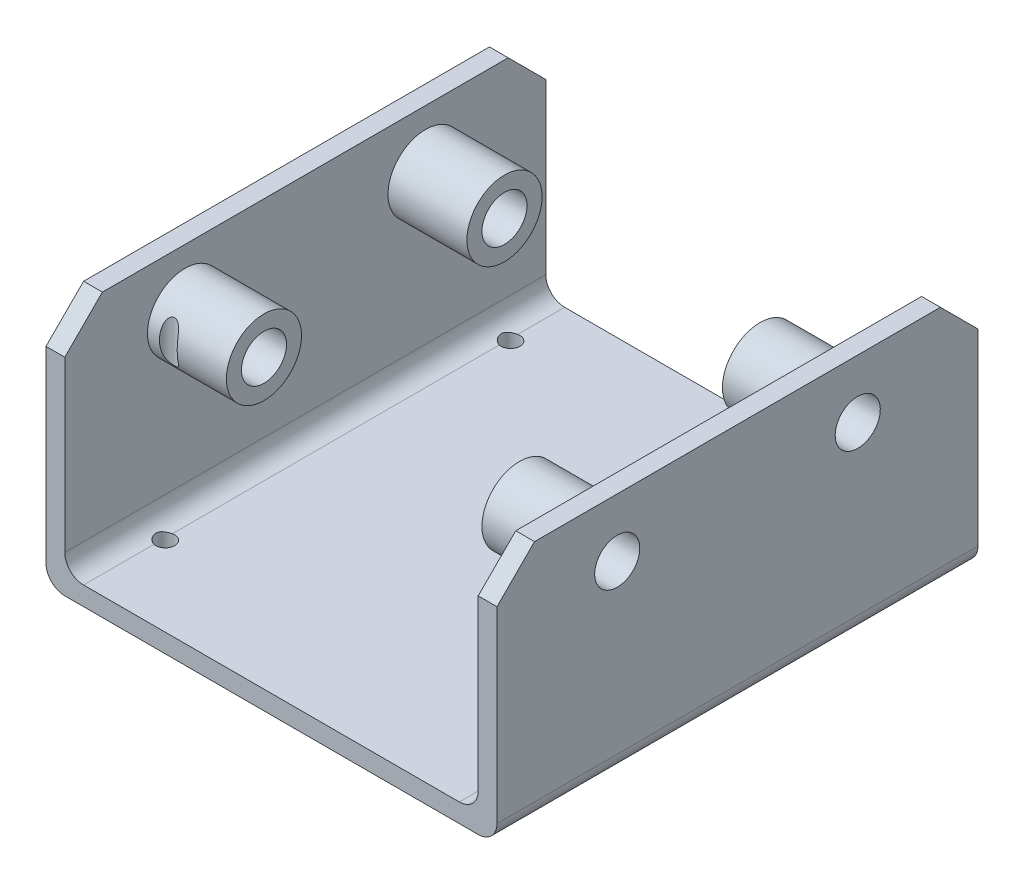
SolidWorks part; units mm, degrees
material "6061 Alloy"
ref_plane "Front Plane" through (0, 0, 0) normal (0, 0, 1) x (1, 0, 0)
ref_plane "Top Plane" through (0, 0, 0) normal (0, 1, 0) x (1, 0, 0)
ref_plane "Right Plane" through (0, 0, 0) normal (1, 0, 0) x (0, 0, -1)
sketch "Sketch2" plane through (0, 0, 0) normal (0, 0, 1) x (1, 0, 0)
  line L2 (-55, 30) -> (-55, -30)
  line L3 (-55, -30) -> (55, -30)
  line L4 (55, 30) -> (55, -30)
  line L5 (-55, 30) -> (55, -30) construction
  line L6 (-55, -30) -> (55, 30) construction
  line L7 (60, 30) -> (60, -35)
  line L8 (-60, -35) -> (60, -35)
  line L9 (-60, 30) -> (-60, -35)
  line L10 (-60, 30) -> (-55, 30)
  line L11 (-60, 35) -> (-60, -35) construction
  line L12 (-60, 35) -> (60, 35) construction
  line L13 (-55, 30) -> (55, 30) construction
  line L14 (55, 30) -> (60, 30)
  line L15 (60, 35) -> (60, -35) construction
  point P0 (0, 0)
  dimension "D1" = 110
  dimension "D2" = 60
  dimension "D3" = 5
extrude "Boss-Extrude1" add sketch "Sketch2" along normal blind 128
fillet "Fillet1" radius 5 4 edges at (-55, -30, 64) (55, -30, 64) (60, -35, 64) (-60, -35, 64)
chamfer "Chamfer1" distance 10 angle 45 4 edges at (57.5, 30, 0) (57.5, 30, 128) (-57.5, 30, 0) (-57.5, 30, 128)
sketch "Sketch3" plane through (60, 0, 0) normal (1, 0, 0) x (0, 0, -1)
  line L0 (-128, -30) -> (-128, 20) construction
  line L1 (-64, 30) -> (-64, -5.6141) construction
  line L2 (-118, 30) -> (-10, 30) construction
  circle A0 centre (-96, 14.4852) radius 6
  circle A1 centre (-32, 14.4852) radius 6
  dimension "D2" = 12
  dimension "D1" = 32
extrude "Cut-Extrude1" cut sketch "Sketch3" against normal through all
sketch "Sketch5" plane through (55, 0, 0) normal (-1, 0, 0) x (0, 0, 1)
  circle A0 centre (32, 14.4852) radius 10
  circle A1 centre (96, 14.4852) radius 10
  dimension "D1" = 20
  dimension "D2" = 20
extrude "Boss-Extrude2" add sketch "Sketch5" along normal blind 21
sketch "Sketch6" plane through (-55, 0, 0) normal (1, 0, 0) x (0, 0, -1)
  circle A0 centre (-32, 14.4852) radius 10
  circle A1 centre (-96, 14.4852) radius 10
  dimension "D1" = 20
  dimension "D2" = 20
extrude "Boss-Extrude3" add sketch "Sketch6" along normal blind 21
sketch "Sketch7" plane through (-55, 0, 0) normal (-1, 0, 0) x (0, 0, 1)
  circle A0 centre (32, 14.4852) radius 6
  circle A1 centre (96, 14.4852) radius 6
extrude "Cut-Extrude2" cut sketch "Sketch7" against normal through all both and the other way through all
sketch "Sketch8" plane through (0, -35, 0) normal (0, -1, 0) x (1, 0, 0)
  circle A0 centre (49.4503, 14.9291) radius 2.5
  circle A1 centre (-49.4503, 14.9291) radius 2.5
  circle A2 centre (-49.4503, 106.8213) radius 2.5
  circle A3 centre (49.4503, 106.8213) radius 2.5
extrude "Cut-Extrude3" cut sketch "Sketch8" against normal through all
